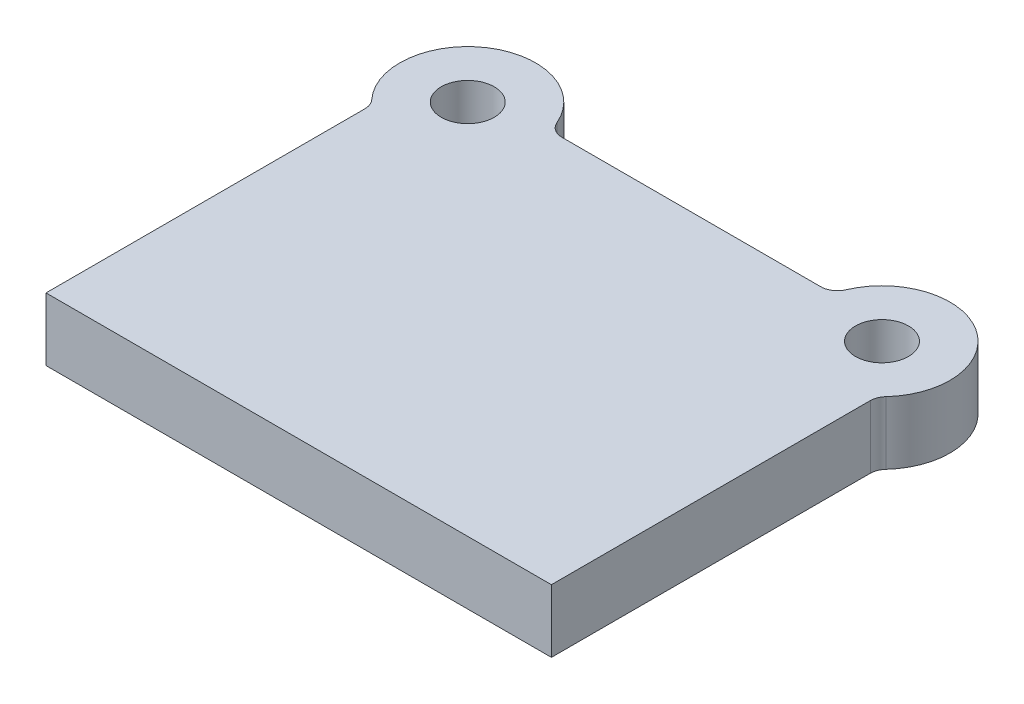
SolidWorks part; units mm, degrees
ref_plane "Front Plane" through (0, 0, 0) normal (0, 0, 1) x (1, 0, 0)
ref_plane "Top Plane" through (0, 0, 0) normal (0, 1, 0) x (1, 0, 0)
ref_plane "Right Plane" through (0, 0, 0) normal (1, 0, 0) x (0, 0, -1)
sketch "Sketch1" plane through (0, 0, 0) normal (0, 1, 0) x (1, 0, 0)
  line L0 (152.5, 0) -> (-152.5, 0)
  line L1 (-152.5, 0) -> (-152.5, 196.5903)
  line L2 (0, 0) -> (0, 237) construction
  line L3 (85.2382, 237) -> (-85.2382, 237)
  line L4 (152.5, 0) -> (152.5, 196.5903)
  arc A0 (-85.2382, 237) -> (-152.5, 196.5903) centre (-125, 227) ccw
  circle A1 centre (-125, 227) radius 16
  circle A2 centre (125, 227) radius 16
  arc A3 (85.2382, 237) -> (152.5, 196.5903) centre (125, 227) cw
  point P2 (0, 0)
  dimension "D1" = 227
  dimension "D2" = 305
  dimension "D3" = 250
  dimension "D4" = 82
  dimension "D5" = 32
  dimension "D6" = 237
extrude "Boss-Extrude1" add sketch "Sketch1" along normal blind 38
fillet "Fillet2" radius 10 4 edges at (152.5, 19, -196.5903) (-152.5, 19, -196.5903) (85.2382, 19, -237) (-85.2382, 19, -237)
